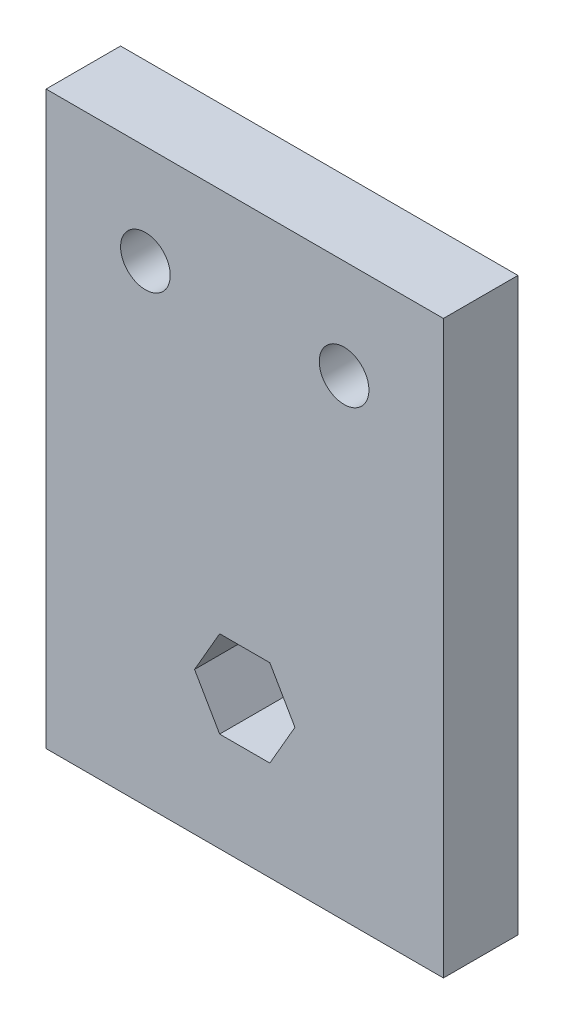
SolidWorks part; units mm, degrees
material "ABS"
ref_plane "Front Plane" through (0, 0, 0) normal (0, 0, 1) x (1, 0, 0)
ref_plane "Top Plane" through (0, 0, 0) normal (0, 1, 0) x (1, 0, 0)
ref_plane "Right Plane" through (0, 0, 0) normal (1, 0, 0) x (0, 0, -1)
sketch "Sketch2" plane through (0, 0, 0) normal (0, 0, 1) x (1, 0, 0)
  line L0 (25.4, 73.025) -> (25.4, -36.5125) construction
  line L1 (0, 0) -> (50.8, 0)
  line L2 (0, 0) -> (0, 73.025)
  line L3 (0, 73.025) -> (50.8, 73.025)
  line L4 (50.8, 0) -> (50.8, 73.025)
  line L6 (31.8158, 18.2562) -> (28.6079, 23.8125)
  line L7 (28.6079, 23.8125) -> (22.1921, 23.8125)
  line L8 (22.1921, 23.8125) -> (18.9842, 18.2562)
  line L9 (18.9842, 18.2562) -> (22.1921, 12.7)
  line L10 (22.1921, 12.7) -> (28.6079, 12.7)
  line L11 (28.6079, 12.7) -> (31.8158, 18.2562)
  circle A0 centre (12.7, 60.325) radius 3.175
  circle A1 centre (38.1, 60.325) radius 3.175
  circle A2 centre (25.4, 18.2562) radius 5.5562 construction
  dimension "D3" = 6.35
  dimension "D1" = 50.8
  dimension "D2" = 73.025
  dimension "D4" = 12.7
  dimension "D5" = 12.7
  dimension "D6" = 18.2562
extrude "Extrude1" add sketch "Sketch2" along normal blind 9.525
